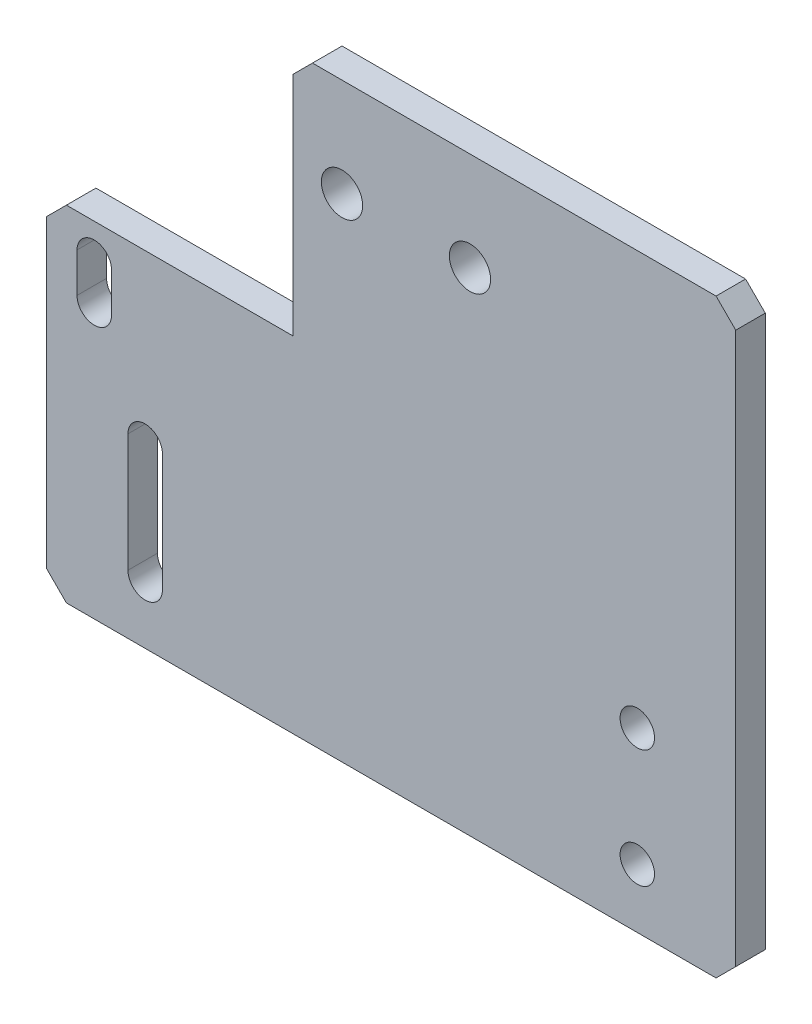
SolidWorks part; units mm, degrees
ref_plane "Front Plane" through (0, 0, 0) normal (0, 0, 1) x (1, 0, 0)
ref_plane "Top Plane" through (0, 0, 0) normal (0, 1, 0) x (1, 0, 0)
ref_plane "Right Plane" through (0, 0, 0) normal (1, 0, 0) x (0, 0, -1)
sketch "Sketch1" plane through (0, 0, 0) normal (0, 0, 1) x (1, 0, 0)
  line L0 (-11.8304, 26.8438) -> (33.1696, 26.8438)
  line L1 (33.1696, 26.8438) -> (33.1696, -33.1562)
  line L2 (33.1696, -33.1562) -> (-36.8304, -33.1563)
  line L3 (-36.8304, -33.1563) -> (-36.8304, 1.8437)
  line L4 (-36.8304, 1.8437) -> (-11.8304, 1.8437)
  line L5 (-11.8304, 1.8437) -> (-11.8304, 26.8438)
  line L6 (-25.0804, -15.1563) -> (-25.0804, -27.1563)
  line L7 (-28.5804, -15.1563) -> (-28.5804, -27.1563)
  line L8 (-33.75, -1.558) -> (-33.75, -5.558)
  line L10 (-30.25, -1.558) -> (-30.25, -5.558)
  arc A0 (-28.5804, -27.1563) -> (-25.0804, -27.1563) centre (-26.8304, -27.1563) ccw
  arc A1 (-25.0804, -15.1563) -> (-28.5804, -15.1563) centre (-26.8304, -15.1563) ccw
  circle A2 centre (23.1696, -15.1563) radius 1.75
  circle A3 centre (23.1696, -27.1563) radius 1.75
  circle A4 centre (6.1696, 16.8438) radius 2.0963
  circle A5 centre (-6.8304, 16.8438) radius 2.0963
  arc A6 (-30.25, -1.558) -> (-33.75, -1.558) centre (-32, -1.558) ccw
  arc A7 (-33.75, -5.558) -> (-30.25, -5.558) centre (-32, -5.558) ccw
  dimension "D5" = 3.5
  dimension "D6" = 10
  dimension "D7" = 10
  dimension "D8" = 5
  dimension "D9" = 13
  dimension "D10" = 10
  dimension "D1" = 45
  dimension "D2" = 70
  dimension "D3" = 35
  dimension "D4" = 60
  dimension "D11" = 3.5
  dimension "D12" = 12
  dimension "D13" = 6
extrude "Boss-Extrude1" add sketch "Sketch1" along normal blind 3
chamfer "Chamfer1" distance 2 angle 45 5 edges at (-36.8304, 1.8437, 1.5) (-36.8304, -33.1563, 1.5) (33.1696, -33.1562, 1.5) (33.1696, 26.8438, 1.5) (-11.8304, 26.8438, 1.5)
